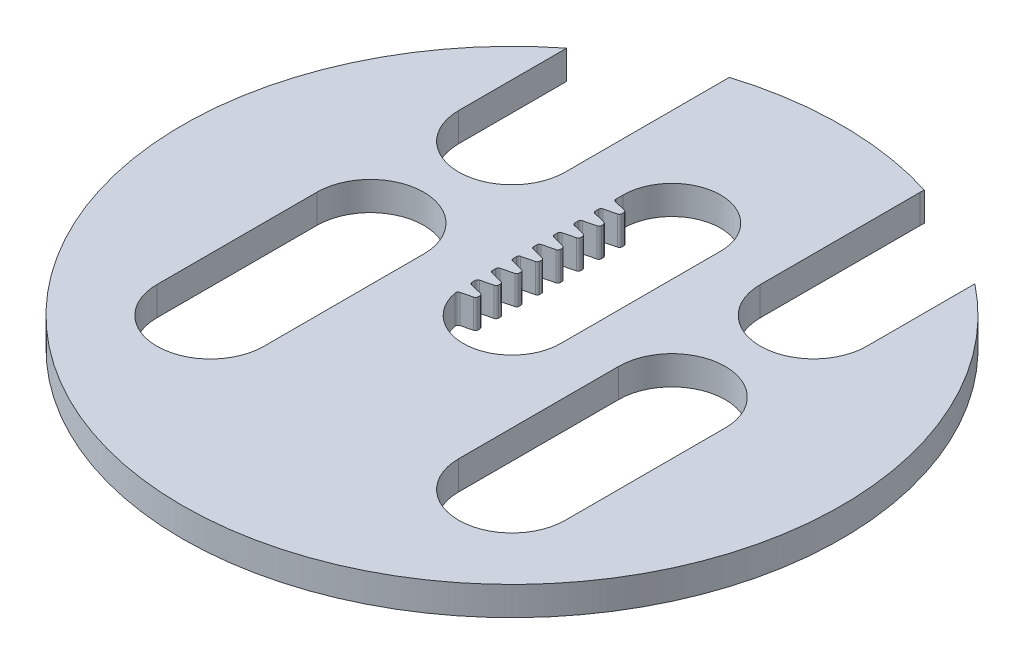
SolidWorks part; units mm, degrees
ref_plane "Front Plane" through (0, 0, 0) normal (0, 0, 1) x (1, 0, 0)
ref_plane "Top Plane" through (0, 0, 0) normal (0, 1, 0) x (1, 0, 0)
ref_plane "Right Plane" through (0, 0, 0) normal (1, 0, 0) x (0, 0, -1)
sketch "Sketch3" plane through (0, 0, 0) normal (0, -1, 0) x (1, 0, 0)
  line L0 (0, 0) -> (0, -19.05) construction
  line L1 (5.8, 0) -> (5.8, -19.05)
  line L2 (-5.8, 0) -> (-5.8, -19.05)
  line L3 (-17.9605, -37.0105) -> (17.9605, -1.0895) construction
  line L4 (-17.9605, -1.0895) -> (17.9605, -37.0105) construction
  line L5 (-17.9605, -1.0895) -> (17.9605, -1.0895) construction
  line L6 (-17.9605, -1.0895) -> (-17.9605, 17.9605) construction
  line L7 (-24.3305, -1.0895) -> (-24.3305, 17.9605)
  line L8 (-11.5905, -1.0895) -> (-11.5905, 17.9605)
  line L9 (-17.9605, -37.0105) -> (-17.9605, -17.9605) construction
  line L10 (-24.3105, -37.0105) -> (-24.3105, -17.9605)
  line L11 (-11.6105, -37.0105) -> (-11.6105, -17.9605)
  line L12 (17.9605, -1.0895) -> (17.9605, 17.9605) construction
  line L13 (11.6105, -1.0895) -> (11.6105, 17.9605)
  line L14 (24.3105, -1.0895) -> (24.3105, 17.9605)
  line L15 (17.9605, -37.0105) -> (17.9605, -17.9605) construction
  line L16 (11.6105, -37.0105) -> (11.6105, -17.9605)
  line L17 (24.3105, -37.0105) -> (24.3105, -17.9605)
  circle A0 centre (0, 0) radius 39.2557
  arc A1 (5.8, 0) -> (-5.8, 0) centre (0, 0) ccw
  arc A2 (-5.8, -19.05) -> (5.8, -19.05) centre (0, -19.05) ccw
  arc A3 (-24.3305, -1.0895) -> (-11.5905, -1.0895) centre (-17.9605, -1.0895) ccw
  arc A4 (-11.5905, 17.9605) -> (-24.3305, 17.9605) centre (-17.9605, 17.9605) ccw
  arc A5 (-24.3105, -37.0105) -> (-11.6105, -37.0105) centre (-17.9605, -37.0105) ccw
  arc A6 (-11.6105, -17.9605) -> (-24.3105, -17.9605) centre (-17.9605, -17.9605) ccw
  arc A7 (11.6105, -1.0895) -> (24.3105, -1.0895) centre (17.9605, -1.0895) ccw
  arc A8 (24.3105, 17.9605) -> (11.6105, 17.9605) centre (17.9605, 17.9605) ccw
  arc A9 (11.6105, -37.0105) -> (24.3105, -37.0105) centre (17.9605, -37.0105) ccw
  arc A10 (24.3105, -17.9605) -> (11.6105, -17.9605) centre (17.9605, -17.9605) ccw
  point P5 (0, -9.525)
  point P10 (-17.9605, 8.4355)
  point P13 (0, -19.05)
  point P16 (0, -19.05)
  point P22 (-17.9605, -27.4855)
  point P28 (17.9605, 8.4355)
  point P34 (17.9605, -27.4855)
  dimension "D1" = 78.5114
  dimension "D3" = 5.8
  dimension "D8" = 6.37
  dimension "D10" = 6.35
  dimension "D13" = 6.35
  dimension "D14" = 6.35
  dimension "D2" = 19.05
  dimension "D4" = 45
  dimension "D5" = 45
  dimension "D6" = 50.8
extrude "Boss-Extrude1" add sketch "Sketch3" along normal blind 3.175 and the other way blind 0.254 contours L17 A10 L16 A0 L11 A6 L10 L2 A2 L1 A1 L8 A4 L7 A3 L14 A8 L13 A7
sketch "Sketch4" plane through (0, 0.254, 0) normal (0, 1, 0) x (1, 0, 0)
  line L0 (-5.8, 0) -> (-3.94, 0) construction
  line L1 (-3.94, -0.34) -> (-3.94, 0.34)
  line L2 (-3.94, 0.34) -> (-5.8, 0.8038)
  line L3 (-5.8, 0) -> (-5.8, 19.05) construction
  line L8 (-5.8, 0.8038) -> (-5.8, -0.8038)
  line L9 (-5.8, -0.8038) -> (-3.94, -0.34)
  point P7 (-3.94, 0)
  dimension "D3" = 76
  dimension "D1" = 1.86
  dimension "D2" = 0.34
extrude "Boss-Extrude2" add sketch "Sketch4" against normal up to surface (3.429 mm away) up to face at (0, -3.175, -9.525)
pattern_linear "LPattern1" count 8 spacing 2.45 along (0, 0, -1) of "Boss-Extrude2"
fillet "Fillet1" radius 0.3 32 edges at (-3.94, -1.4605, 0.34) (-5.8, -1.4605, -1.6462) (-3.94, -1.4605, -2.11) (-3.94, -1.4605, -2.79) (-5.8, -1.4605, -3.2538) (-5.8, -1.4605, -4.0962) (-3.94, -1.4605, -4.56) (-3.94, -1.4605, -5.24) (-5.8, -1.4605, -5.7038) (-5.8, -1.4605, -6.5462) (-3.94, -1.4605, -7.01) (-3.94, -1.4605, -7.69) (-5.8, -1.4605, -8.1538) (-5.8, -1.4605, -8.9962) (-3.94, -1.4605, -9.46) (-3.94, -1.4605, -10.14) (-5.8, -1.4605, -10.6038) (-5.8, -1.4605, -11.4462) (-3.94, -1.4605, -11.91) (-3.94, -1.4605, -12.59) (-5.8, -1.4605, -13.0538) (-5.8, -1.4605, -13.8962) (-3.94, -1.4605, -14.36) (-3.94, -1.4605, -15.04) (-5.8, -1.4605, -15.5038) (-5.8, -1.4605, -16.3462) (-3.94, -1.4605, -16.81) (-3.94, -1.4605, -17.49) (-5.8, -1.4605, -17.9538) (-5.7459, -1.4605, 0.7903) (-5.8, -1.4605, -0.8038) (-3.94, -1.4605, -0.34)
equation "\"AIRFRAME_OD\"= 3.091in"
equation "\"AIRFRAME_ID\"= 3.00in"
equation "\"FLAT_T\"= 0.125in"
equation "\"COUPLER_OD\"= 2.998in"
equation "\"COUPLER_ID\"= 2.875in"
equation "\"NOSE_EXP_L\"= 3.5in"
equation "\"NOSE_SHOULDER_L\"= 5in"
equation "\"MAIN_L\"= 26in"
equation "\"RECO_COUP_L\"= 6in"
equation "\"RECO_SWITCH_L\"= 1.5in"
equation "\"RECO_ROD_X\"= 1.5in"
equation "\"DROGUE_L\"= 14in"
equation "\"ATS_FORE_COUP_L\"= 4in"
equation "\"ATS_AFT_COUP_L\"= 4in"
equation "\"ATS_ROD_X\"= 2in"
equation "\"LOWER_L\"= 16in"
equation "\"FIN_ROOT\"= 5in"
equation "\"FIN_X\"= 0.75in"
equation "\"FIN_N\"= 4"
equation "\"MOTOR_OD\"= 2.25in"
equation "\"MOTOR_ID\"= 2.126in"
equation "\"MOTOR_L\"= 8in"
equation "\"MOTOR_LOWER_X\"= 0.5in"
equation "\"CR_AFT_X\"= 0.5in"
equation "\"CR_FORE_X\"= 6in"
equation "\"D1@Boss-Extrude1\"=\"FLAT_T\""
equation "\"D1@Sketch3\"=\"AIRFRAME_OD\""
equation "\"D6@Sketch3\"=\"ATS_ROD_X\""
